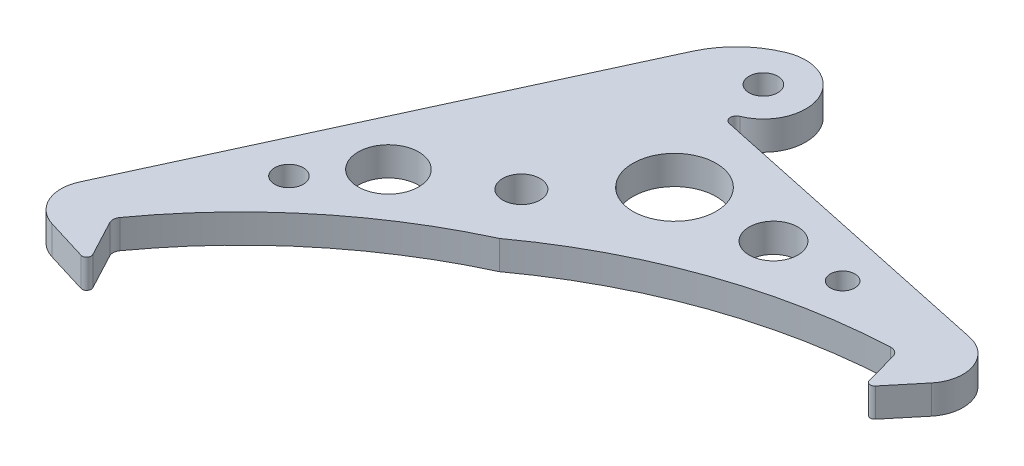
SolidWorks part; units mm, degrees
ref_plane "Front Plane" through (0, 0, 0) normal (0, 0, 1) x (1, 0, 0)
ref_plane "Top Plane" through (0, 0, 0) normal (0, 1, 0) x (1, 0, 0)
ref_plane "Right Plane" through (0, 0, 0) normal (1, 0, 0) x (0, 0, -1)
sketch "Sketch1" plane through (0, 0, 0) normal (0, 1, 0) x (1, 0, 0)
  line L0 (7.7282, 79.6258) -> (8.4438, 86.9988) construction
  line L1 (7.7282, 79.6258) -> (6.2992, 88.205) construction
  line L2 (6.2992, 88.205) -> (-0.5, 79.9984) construction
  line L3 (-0.5, 79.9984) -> (0, 0) construction
  line L4 (15.8744, 78.4092) -> (15.3351, 87.0899) construction
  line L5 (15.3351, 87.0899) -> (7.7282, 79.6258) construction
  line L6 (23.8524, 76.3614) -> (24.2085, 85.0515) construction
  line L7 (24.2085, 85.0515) -> (15.8744, 78.4092) construction
  line L8 (31.5775, 73.5041) -> (32.8253, 82.1116) construction
  line L9 (32.8253, 82.1116) -> (23.8524, 76.3614) construction
  line L10 (38.9679, 69.8677) -> (41.0941, 78.3012) construction
  line L11 (41.0941, 78.3012) -> (31.5775, 73.5041) construction
  line L12 (45.9453, 65.4907) -> (48.9273, 73.6609) construction
  line L13 (48.9273, 73.6609) -> (38.9679, 69.8677) construction
  line L14 (52.4356, 60.4195) -> (56.2419, 68.2397) construction
  line L15 (56.2419, 68.2397) -> (45.9453, 65.4907) construction
  line L16 (58.37, 54.7077) -> (62.9603, 62.0952) construction
  line L17 (62.9603, 62.0952) -> (52.4356, 60.4195) construction
  line L18 (63.6858, 48.4161) -> (69.0113, 55.2924) construction
  line L19 (69.0113, 55.2924) -> (58.37, 54.7077) construction
  line L20 (68.3264, 41.6113) -> (74.3307, 47.9036) construction
  line L21 (74.3307, 47.9036) -> (63.6858, 48.4161) construction
  line L22 (72.2428, 34.3653) -> (78.8623, 40.0069) construction
  line L23 (78.8623, 40.0069) -> (68.3264, 41.6113) construction
  line L24 (75.3934, 26.7551) -> (82.5578, 31.6862) construction
  line L25 (82.5578, 31.6862) -> (72.2428, 34.3653) construction
  line L26 (77.7448, 18.8613) -> (85.3783, 23.0296) construction
  line L27 (85.3783, 23.0296) -> (75.3934, 26.7551) construction
  line L28 (79.2721, 10.7675) -> (87.2937, 14.1288) construction
  line L29 (87.2937, 14.1288) -> (77.7448, 18.8613) construction
  line L30 (79.959, 2.5596) -> (88.2837, 5.0783) construction
  line L31 (88.2837, 5.0783) -> (79.2721, 10.7675) construction
  line L32 (79.7984, -5.6754) -> (88.338, -4.026) construction
  line L33 (88.338, -4.026) -> (79.959, 2.5596) construction
  line L34 (78.7919, -13.8503) -> (87.4558, -13.0877) construction
  line L35 (87.4558, -13.0877) -> (79.7984, -5.6754) construction
  line L36 (76.9502, -21.8783) -> (85.6466, -22.0106) construction
  line L37 (85.6466, -22.0106) -> (78.7919, -13.8503) construction
  line L38 (74.2928, -29.6745) -> (82.9295, -30.7002) construction
  line L39 (82.9295, -30.7002) -> (76.9502, -21.8783) construction
  line L40 (70.8479, -37.1561) -> (79.3334, -39.0644) construction
  line L41 (79.3334, -39.0644) -> (74.2928, -29.6745) construction
  line L42 (66.652, -44.2438) -> (74.8962, -47.0145) construction
  line L43 (74.8962, -47.0145) -> (70.8479, -37.1561) construction
  line L44 (61.7495, -50.8625) -> (69.6652, -54.4662) construction
  line L45 (69.6652, -54.4662) -> (66.652, -44.2438) construction
  line L46 (56.1925, -56.9421) -> (63.6957, -61.3406) construction
  line L47 (63.6957, -61.3406) -> (61.7495, -50.8625) construction
  line L48 (50.0398, -62.4181) -> (57.051, -67.5647) construction
  line L49 (57.051, -67.5647) -> (56.1925, -56.9421) construction
  line L50 (43.3567, -67.2324) -> (49.8016, -73.0727) construction
  line L51 (49.8016, -73.0727) -> (50.0398, -62.4181) construction
  line L52 (36.214, -71.334) -> (42.0242, -77.806) construction
  line L53 (42.0242, -77.806) -> (43.3567, -67.2324) construction
  line L54 (28.6875, -74.6795) -> (33.8014, -81.7146) construction
  line L55 (33.8014, -81.7146) -> (36.214, -71.334) construction
  line L56 (20.8568, -77.2334) -> (25.2202, -84.757) construction
  line L57 (25.2202, -84.757) -> (28.6875, -74.6795) construction
  line L58 (12.805, -78.9685) -> (16.3718, -86.9009) construction
  line L59 (16.3718, -86.9009) -> (20.8568, -77.2334) construction
  line L60 (4.6176, -79.8666) -> (7.3498, -88.1237) construction
  line L61 (7.3498, -88.1237) -> (12.805, -78.9685) construction
  line L62 (-3.6189, -79.9181) -> (-1.7502, -88.4124) construction
  line L63 (-1.7502, -88.4124) -> (4.6176, -79.8666) construction
  line L64 (-11.817, -79.1224) -> (-10.8315, -87.7638) construction
  line L65 (-10.8315, -87.7638) -> (-3.6189, -79.9181) construction
  line L66 (-19.8898, -77.488) -> (-19.7981, -86.1849) construction
  line L67 (-19.7981, -86.1849) -> (-11.817, -79.1224) construction
  line L68 (-27.7518, -75.0323) -> (-28.5548, -83.6925) construction
  line L69 (-28.5548, -83.6925) -> (-19.8898, -77.488) construction
  line L70 (-35.3196, -71.7811) -> (-37.0088, -80.3129) construction
  line L71 (-37.0088, -80.3129) -> (-27.7518, -75.0323) construction
  line L72 (-42.513, -67.7691) -> (-45.0705, -76.0819) construction
  line L73 (-45.0705, -76.0819) -> (-35.3196, -71.7811) construction
  line L74 (-49.2557, -63.0387) -> (-52.6544, -71.0445) construction
  line L75 (-52.6544, -71.0445) -> (-42.513, -67.7691) construction
  line L76 (-55.4764, -57.64) -> (-59.6802, -65.254) construction
  line L77 (-59.6802, -65.254) -> (-49.2557, -63.0387) construction
  line L78 (-61.1089, -51.6304) -> (-66.0734, -58.7717) construction
  line L79 (-66.0734, -58.7717) -> (-55.4764, -57.64) construction
  line L80 (-66.0937, -45.0735) -> (-71.7662, -51.6665) construction
  line L81 (-71.7662, -51.6665) -> (-61.1089, -51.6304) construction
  line L82 (-70.3779, -38.0387) -> (-76.6982, -44.0136) construction
  line L83 (-76.6982, -44.0136) -> (-66.0937, -45.0735) construction
  line L84 (-73.9161, -30.6008) -> (-80.8172, -35.8941) construction
  line L85 (-80.8172, -35.8941) -> (-70.3779, -38.0387) construction
  line L86 (-76.6707, -22.8385) -> (-84.0795, -27.3942) construction
  line L87 (-84.0795, -27.3942) -> (-73.9161, -30.6008) construction
  line L88 (-78.6127, -14.8341) -> (-86.4506, -18.6039) construction
  line L89 (-86.4506, -18.6039) -> (-76.6707, -22.8385) construction
  line L90 (-79.7213, -6.6724) -> (-87.9053, -9.6163) construction
  line L91 (-87.9053, -9.6163) -> (-78.6127, -14.8341) construction
  line L92 (-79.9848, 1.56) -> (-88.4281, -0.5268) construction
  line L93 (-88.4281, -0.5268) -> (-79.7213, -6.6724) construction
  line L94 (-79.4005, 9.7758) -> (-88.0136, 8.5682) construction
  line L95 (-88.0136, 8.5682) -> (-79.9848, 1.56) construction
  line L96 (-77.9745, 17.888) -> (-86.6661, 17.5724) construction
  line L97 (-86.6661, 17.5724) -> (-79.4005, 9.7758) construction
  line L98 (-75.7219, 25.8106) -> (-84.4, 26.3904) construction
  line L99 (-84.4, 26.3904) -> (-77.9745, 17.888) construction
  line L100 (-72.6667, 33.4596) -> (-81.2392, 34.9286) construction
  line L101 (-81.2392, 34.9286) -> (-75.7219, 25.8106) construction
  line L102 (-68.8412, 40.754) -> (-77.2172, 43.0966) construction
  line L103 (-77.2172, 43.0966) -> (-72.6667, 33.4596) construction
  line L104 (-64.286, 47.6163) -> (-72.3767, 50.8077) construction
  line L105 (-72.3767, 50.8077) -> (-68.8412, 40.754) construction
  line L106 (-59.0493, 53.9739) -> (-66.769, 57.9803) construction
  line L107 (-66.769, 57.9803) -> (-64.286, 47.6163) construction
  line L108 (-53.1867, 59.7593) -> (-60.4535, 64.5382) construction
  line L109 (-60.4535, 64.5382) -> (-59.0493, 53.9739) construction
  line L110 (-46.7603, 64.9113) -> (-53.4972, 70.4121) construction
  line L111 (-53.4972, 70.4121) -> (-53.1867, 59.7593) construction
  line L112 (-39.8382, 69.3752) -> (-45.9738, 75.5395) construction
  line L113 (-45.9738, 75.5395) -> (-46.7603, 64.9113) construction
  line L114 (-32.4938, 73.1037) -> (-37.9631, 79.8662) construction
  line L115 (-37.9631, 79.8662) -> (-39.8382, 69.3752) construction
  line L116 (-24.805, 76.0573) -> (-29.55, 83.3463) construction
  line L117 (-29.55, 83.3463) -> (-32.4938, 73.1037) construction
  line L118 (-16.8533, 78.2046) -> (-20.8236, 85.9429) construction
  line L119 (-20.8236, 85.9429) -> (-24.805, 76.0573) construction
  line L120 (-8.7229, 79.523) -> (-11.8765, 87.6285) construction
  line L121 (-11.8765, 87.6285) -> (-16.8533, 78.2046) construction
  line L122 (-0.5, 79.9984) -> (-2.8035, 88.3852) construction
  line L123 (-2.8035, 88.3852) -> (-8.7229, 79.523) construction
  line L124 (-57, 80) -> (-4.4637, 94.4296) construction
  line L125 (-2.6864, 87.959) -> (-0.5, 79.9984)
  line L126 (-0.5, 79.9984) -> (4.6149, 86.1721)
  line L127 (1.2421, 95.8689) -> (-49.2295, 106.597)
  line L128 (0, 0) -> (0, 80) construction
  line L129 (-62.6465, 113.849) -> (-94.5643, 44.533)
  line L130 (-57, 80) -> (82.7543, 80) construction
  line L131 (-90.8716, 36.2866) -> (-82.5794, 33.7466)
  line L132 (-82.5794, 33.7466) -> (-85.7042, 43.381)
  line L133 (-57, 80) -> (0, 0) construction
  line L134 (-57, 80) -> (-14.7578, -8.6826) construction
  line L135 (-14.7578, -8.6826) -> (-82.5794, 33.7466) construction
  line L136 (-57, 80) -> (-7.3789, -4.3413) construction
  line L137 (-14.7578, -8.6826) -> (0, 0) construction
  circle A0 centre (0, 0) radius 80 construction
  circle A1 centre (-57, 80) radius 3.1
  arc A2 (-51.7907, 71.1458) -> (-2.6864, 87.959) centre (0, 0) cw
  arc A3 (-51.7907, 71.1458) -> (-85.7042, 43.381) centre (-14.7578, -8.6826) ccw
  arc A4 (4.6149, 86.1721) -> (1.2421, 95.8689) centre (-0.0054, 90) ccw
  circle A5 centre (-52, 115) radius 2.375
  arc A6 (-49.3939, 108.5032) -> (-54.6061, 121.4968) centre (-52, 115) ccw
  arc A7 (-49.2295, 106.597) -> (-49.3939, 108.5032) centre (-49.0216, 107.5751) cw
  arc A8 (-54.6061, 121.4968) -> (-62.6465, 113.849) centre (-49.0216, 107.5751) ccw
  arc A9 (-90.8716, 36.2866) -> (-94.5643, 44.533) centre (-89.1143, 42.0235) cw
  point P212 (0, 0)
  dimension "D1" = 160
  dimension "D4" = 6.2
  dimension "D9" = 88
  dimension "D15" = 4.75
  dimension "D17" = 6
  dimension "D20" = 7
  dimension "D22" = 15
  dimension "D23" = 90
  dimension "D2" = 80
  dimension "D3" = 57
  dimension "D5" = 5.902
  dimension "D6" = 15
  dimension "D7" = 40
  dimension "D10" = 10
  dimension "D11" = 15
  dimension "D12" = 40
  dimension "D13" = 80
  dimension "D14" = 32.5
  dimension "D16" = 90
  dimension "D18" = 35
  dimension "D19" = 5
  dimension "D21" = 12
  dimension "D24" = 0.5
  dimension "D8" = 61
extrude "Boss-Extrude1" add sketch "Sketch1" along normal blind 4.7625
fillet "Fillet1" radius 0.75 2 edges at (-0.5, 2.3813, -79.9984) (-82.5794, 2.3813, -33.7466)
fillet "Fillet2" radius 1.5 2 edges at (-85.7042, 2.3813, -43.381) (-2.6864, 2.3813, -87.959)
sketch "Sketch2" plane through (0, 4.7625, 0) normal (0, 1, 0) x (1, 0, 0)
  line L0 (-83.0749, 35.2375) -> (-86.2444, 41.2061)
  line L2 (-83.0239, 35.1171) -> (-85.4658, 42.6462) construction
  line L3 (-83.0239, 35.1171) -> (-85.2404, 44.0071)
  arc A0 (-83.0239, 35.1171) -> (-83.0749, 35.2375) centre (-83.7373, 34.8857) ccw
  arc A1 (-83.9569, 34.1686) -> (-83.0239, 35.1171) centre (-83.7373, 34.8857) ccw construction
  arc A2 (-86.2444, 41.2061) -> (-86.1363, 42.7869) centre (-84.9196, 41.9096) cw
  arc A3 (-86.1363, 42.7869) -> (-85.2404, 44.0071) centre (-14.7578, -8.6826) cw
  arc A4 (-51.7907, 71.1458) -> (-85.2404, 44.0071) centre (-14.7578, -8.6826) ccw construction
  arc A6 (-85.2404, 44.0071) -> (-85.4658, 42.6462) centre (-84.039, 43.109) ccw construction
  dimension "D1" = 10
extrude "Cut-Extrude1" cut sketch "Sketch2" against normal through all
sketch "Sketch3" plane through (0, 4.7625, 0) normal (0, 1, 0) x (1, 0, 0)
  circle A0 centre (-44.6253, 92.9353) radius 6.8834
  circle A1 centre (-28.7539, 93.4277) radius 4.0273
  circle A2 centre (-17.3321, 93.4277) radius 2.0237
  circle A3 centre (-70.8292, 71.8525) radius 5.0071
  circle A4 centre (-78.105, 62.6871) radius 2.3714
extrude "Cut-Extrude2" cut sketch "Sketch3" against normal through all
